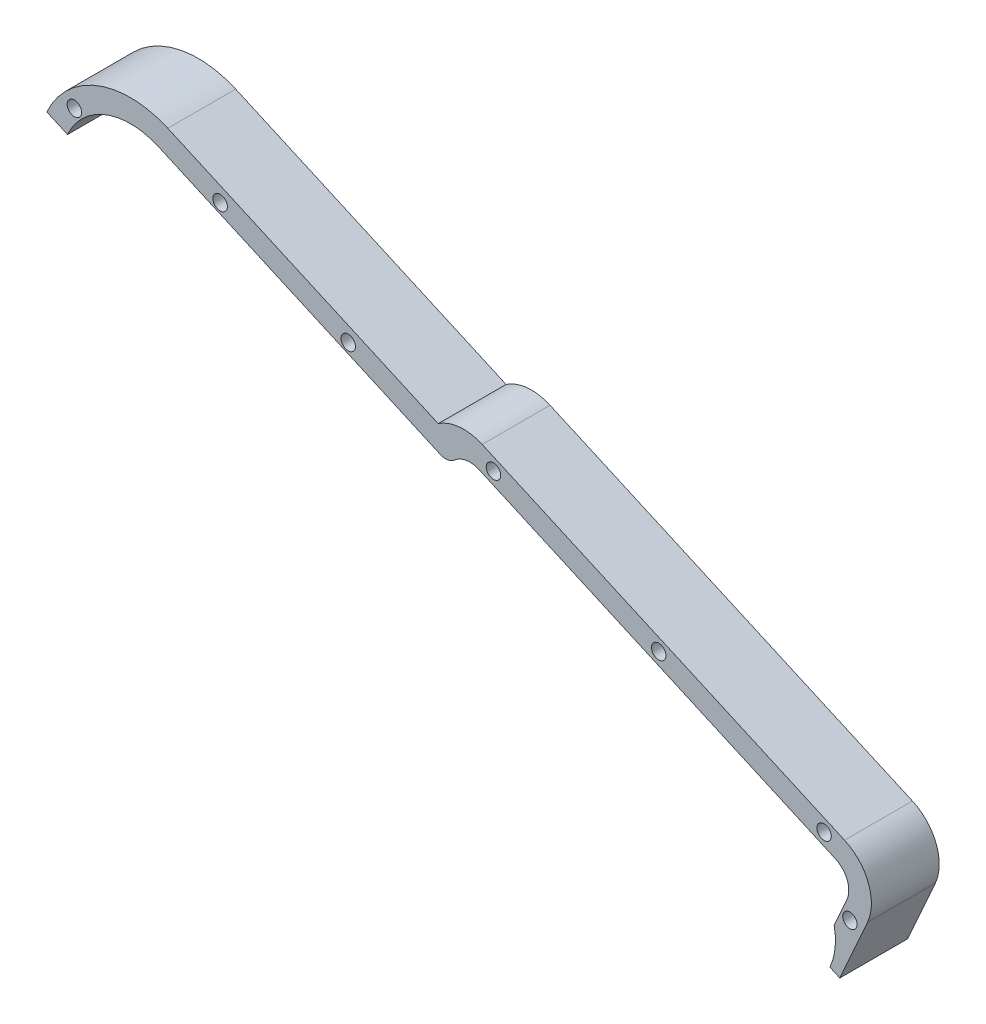
SolidWorks part; units mm, degrees
ref_plane "Front Plane" through (0, 0, 0) normal (0, 0, 1) x (1, 0, 0)
ref_plane "Top Plane" through (0, 0, 0) normal (0, 1, 0) x (1, 0, 0)
ref_plane "Right Plane" through (0, 0, 0) normal (1, 0, 0) x (0, 0, -1)
ref_plane "Plane1" through (0, 0, 15) normal (0, 0, 1) x (1, 0, 0)
sketch "Sketch1" plane through (0, 0, 15) normal (0, 0, 1) x (1, 0, 0)
  line L0 (-72.22, 79.668) -> (-75.0118, 73.4052)
  line L1 (-75.9417, 64.9041) -> (-73.7605, 63.9318)
  line L2 (-73.7605, 63.9318) -> (-67.6532, 77.6322)
  line L3 (-72.7153, 90.8373) -> (-152.817, 126.5446)
  line L4 (-162.5246, 125.6714) -> (-222.2994, 152.3174)
  line L5 (-249.0397, 142.0667) -> (-244.4729, 140.0309)
  line L6 (-224.3351, 147.7506) -> (-162.1035, 120.0094)
  line L7 (-153.4928, 121.3715) -> (-74.7511, 86.2705)
  circle A0 centre (-113.784, 106.4076) radius 1.6
  circle A1 centre (-150.3184, 122.6936) radius 1.6
  circle A2 centre (-77.2496, 90.1215) radius 1.6
  circle A3 centre (-71.5234, 76.0729) radius 1.6
  circle A4 centre (-210.7338, 143.8772) radius 1.6
  circle A5 centre (-182.4196, 131.2555) radius 1.6
  circle A6 centre (-242.9474, 145.8104) radius 1.6
  arc A7 (-75.0118, 73.4052) -> (-75.9417, 64.9041) centre (-88.7288, 70.6043) cw
  arc A8 (-67.6532, 77.6322) -> (-72.7153, 90.8373) centre (-76.7868, 81.7037) ccw
  arc A9 (-152.817, 126.5446) -> (-162.5246, 125.6714) centre (-156.8885, 117.411) ccw
  arc A10 (-222.2994, 152.3174) -> (-249.0397, 142.0667) centre (-230.5442, 133.8219) ccw
  arc A11 (-244.4729, 140.0309) -> (-224.3351, 147.7506) centre (-230.5442, 133.8219) cw
  arc A12 (-162.1035, 120.0094) -> (-158.8745, 120.5202) centre (-160.8821, 122.7495) ccw
  arc A13 (-158.8745, 120.5202) -> (-153.4928, 121.3715) centre (-155.5286, 116.8047) cw
  arc A14 (-74.7511, 86.2705) -> (-72.22, 79.668) centre (-76.7868, 81.7037) cw
extrude "Boss-Extrude1" add sketch "Sketch1" against normal blind 15
